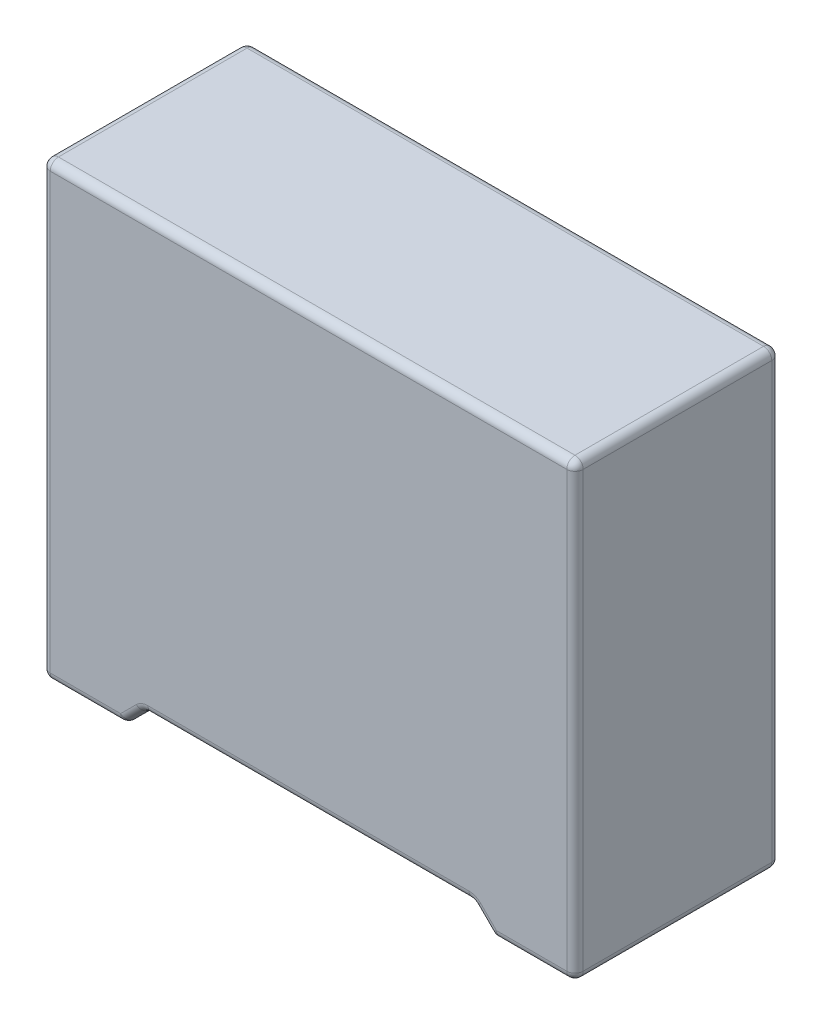
SolidWorks part; units mm, degrees
ref_plane "Front Plane" through (0, 0, 0) normal (0, 0, 1) x (1, 0, 0)
ref_plane "Top Plane" through (0, 0, 0) normal (0, 1, 0) x (1, 0, 0)
ref_plane "Right Plane" through (0, 0, 0) normal (1, 0, 0) x (0, 0, -1)
sketch "Sketch1" plane through (0, 0, 0) normal (0, 1, 0) x (1, 0, 0)
  line L0 (6.5, -2.5) -> (-6.5, 2.5) construction
  line L1 (-6.5, 2.5) -> (6.5, 2.5)
  line L2 (-6.5, 2.5) -> (-6.5, -2.5)
  line L3 (-6.5, -2.5) -> (6.5, -2.5)
  line L4 (6.5, 2.5) -> (6.5, -2.5)
  dimension "D1" = 13
  dimension "D2" = 5
extrude "Boss-Extrude1" add sketch "Sketch1" along normal blind 11
sketch "Sketch2" plane through (0, 0, 2.5) normal (0, 0, 1) x (1, 0, 0)
  line L0 (-4.5, 0) -> (-4, 0.5)
  line L1 (-6.5, 0) -> (6.5, 0) construction
  line L2 (-4, 0.5) -> (4, 0.5)
  line L3 (4, 0.5) -> (4.5, 0)
  line L4 (4.5, 0) -> (4.5, -1.5)
  line L5 (4.5, -1.5) -> (-4.5, -1.5)
  line L6 (-4.5, -1.5) -> (-4.5, 0)
  line L7 (0, 0) -> (0, 0.5) construction
  dimension "D1" = 2
  dimension "D2" = 0.5
  dimension "D3" = 45
  dimension "D4" = 2
extrude "Cut-Extrude1" cut sketch "Sketch2" against normal through all
sketch "Sketch3" plane through (0, 0, 0) normal (0, -1, 0) x (1, 0, 0)
  line L0 (-5, 0) -> (5, 0) construction
  circle A1 centre (-5, 0) radius 0.3
  dimension "D1" = 0.6
  dimension "D2" = 10
fillet "Fillet1" radius 0.2 24 edges at (6.5, 0, 0) (4.25, 0.25, -2.5) (5.5, 0, -2.5) (6.5, 5.5, -2.5) (-5.5, 0, -2.5) (-4.25, 0.25, -2.5) (0, 0.5, -2.5) (-6.5, 5.5, -2.5) (-6.5, 0, 0) (0, 11, -2.5) (6.5, 11, 0) (-6.5, 11, 0) (-6.5, 5.5, 2.5) (0, 11, 2.5) (6.5, 5.5, 2.5) (5.5, 0, 2.5) (4.25, 0.25, 2.5) (0, 0.5, 2.5) (-4.25, 0.25, 2.5) (-5.5, 0, 2.5) (4.5, 0, 0) (-4.5, 0, 0) (-4, 0.5, 0) (4, 0.5, 0)
ref_plane "Plane1" through (-5, 0, 0) normal (1, 0, 0) x (0, 0, -1)
sketch "Sketch5" plane through (-5, 0, 0) normal (1, 0, 0) x (0, 0, -1)
  line L0 (0, 0) -> (0, -0.1)
  line L1 (0.5, -0.6) -> (3, -0.6)
  arc A0 (0, -0.1) -> (0.5, -0.6) centre (0.5, -0.1) ccw
  point P7 (0, -0.6)
  dimension "D3" = 0.5
  dimension "D1" = 0.6
  dimension "D2" = 0.5
sweep "Sweep1" add profiles "Sketch3" path "Sketch5"
mirror "Mirror1" about plane through (0, 0, 0) normal (1, 0, 0) of "Sweep1"
